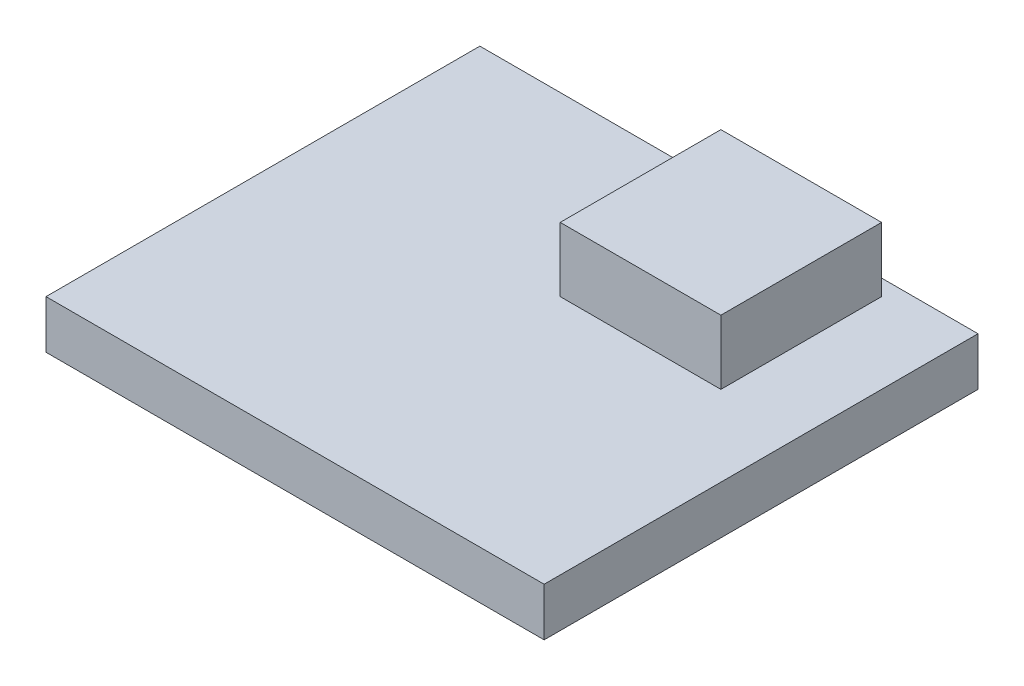
SolidWorks part; units mm, degrees
ref_plane "Front Plane" through (0, 0, 0) normal (0, 0, 1) x (1, 0, 0)
ref_plane "Top Plane" through (0, 0, 0) normal (0, 1, 0) x (1, 0, 0)
ref_plane "Right Plane" through (0, 0, 0) normal (1, 0, 0) x (0, 0, -1)
sketch "Sketch1" plane through (0, 0, 0) normal (0, 1, 0) x (1, 0, 0)
  line L1 (-15.5, 11.7317) -> (15.5, 11.7317)
  line L2 (-15.5, 11.7317) -> (-15.5, -15.2683)
  line L3 (-15.5, -15.2683) -> (15.5, -15.2683)
  line L4 (15.5, 11.7317) -> (15.5, -15.2683)
  dimension "D1" = 31
  dimension "D2" = 27
extrude "Boss-Extrude1" add sketch "Sketch1" along normal blind 3
sketch "Sketch2" plane through (0, 3, 0) normal (0, 1, 0) x (1, 0, 0)
  line L0 (15.5, 11.7317) -> (-15.5, 11.7317) construction
  line L1 (0.5, 10.7317) -> (10.5, 10.7317)
  line L2 (0.5, 10.7317) -> (0.5, 0.7317)
  line L3 (0.5, 0.7317) -> (10.5, 0.7317)
  line L4 (10.5, 10.7317) -> (10.5, 0.7317)
  line L5 (15.5, -15.2683) -> (15.5, 11.7317) construction
  dimension "D1" = 10
  dimension "D2" = 10
  dimension "D3" = 1
  dimension "D4" = 5
extrude "Boss-Extrude2" add sketch "Sketch2" along normal blind 4
